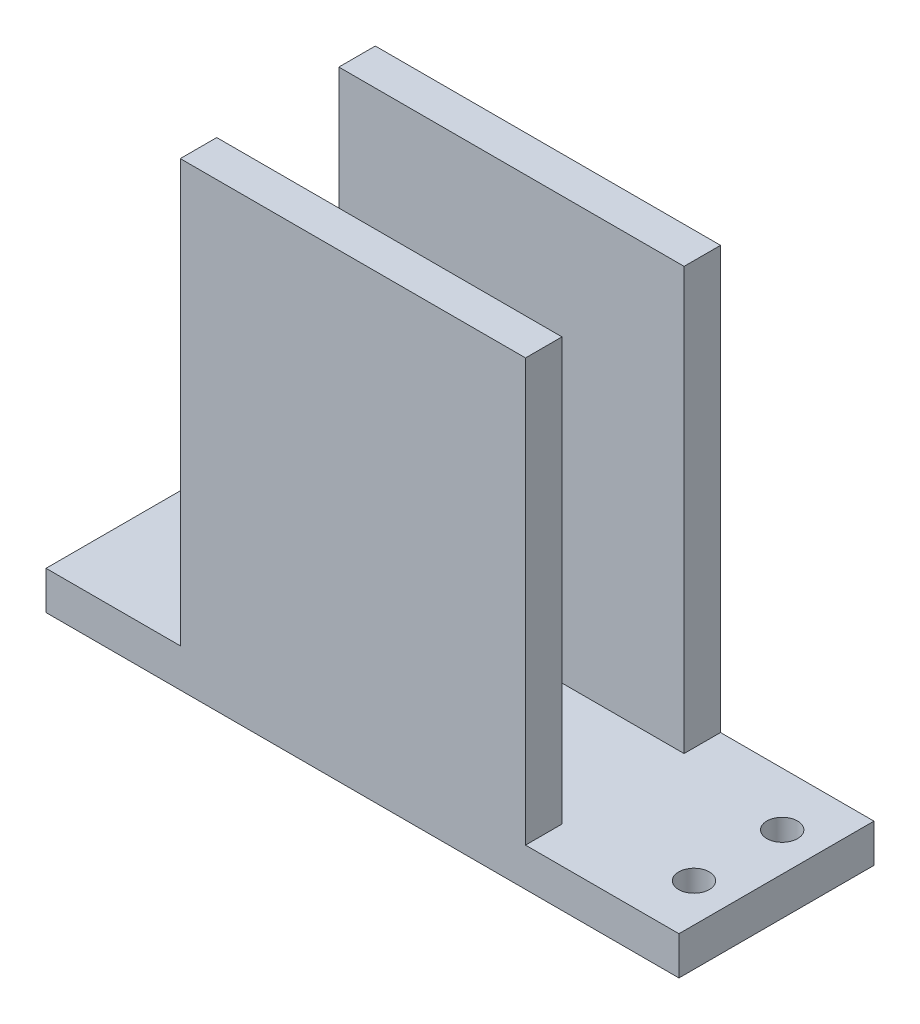
SolidWorks part; units mm, degrees
ref_plane "Front Plane" through (0, 0, 0) normal (0, 0, 1) x (1, 0, 0)
ref_plane "Top Plane" through (0, 0, 0) normal (0, 1, 0) x (1, 0, 0)
ref_plane "Right Plane" through (0, 0, 0) normal (1, 0, 0) x (0, 0, -1)
sketch "Sketch1" plane through (0, 0, 0) normal (0, 1, 0) x (1, 0, 0)
  line L1 (0, 0) -> (165, 0)
  line L2 (0, 0) -> (0, 50.84)
  line L3 (0, 50.84) -> (165, 50.84)
  line L4 (165, 0) -> (165, 50.84)
  dimension "D1" = 165
  dimension "D2" = 50.84
extrude "Boss-Extrude1" add sketch "Sketch1" along normal blind 10
sketch "Sketch2" plane through (0, 10, 0) normal (0, 1, 0) x (1, 0, 0)
  line L0 (0, 25.42) -> (80, 25.42) construction
  line L1 (0, 50.84) -> (0, 0) construction
  line L2 (80, 50.84) -> (80, 0) construction
  line L3 (165, 50.84) -> (0, 50.84) construction
  line L4 (0, 0) -> (165, 0) construction
  line L5 (35, 50.84) -> (125, 50.84)
  line L6 (35, 50.84) -> (35, 40.84)
  line L7 (35, 40.84) -> (125, 40.84)
  line L8 (125, 40.84) -> (125, 50.84)
  line L9 (125, 10) -> (125, 0)
  line L10 (35, 0) -> (125, 0)
  line L11 (35, 0) -> (35, 10)
  line L12 (35, 10) -> (125, 10)
  point P13 (80, 50.84)
  dimension "D1" = 80
  dimension "D2" = 90
  dimension "D3" = 10
extrude "Boss-Extrude2" add sketch "Sketch2" along normal blind 110
sketch "Sketch3" plane through (0, 10, 0) normal (0, 1, 0) x (1, 0, 0)
  line L0 (0, 25.42) -> (165, 25.42) construction
  line L1 (0, 50.84) -> (0, 0) construction
  line L2 (165, 0) -> (165, 50.84) construction
  circle A0 centre (30, 36.92) radius 4
  circle A1 centre (155, 36.92) radius 4
  dimension "D2" = 8
  dimension "D5" = 8
  dimension "D1" = 30
  dimension "D3" = 11.5
  dimension "D4" = 125
extrude "Cut-Extrude1" cut sketch "Sketch3" against normal blind 30
ref_plane "Plane1" through (0, 0, -25.42) normal (0, 0, -1) x (-1, 0, 0)
mirror "Mirror1" about plane through (0, 0, -25.42) normal (0, 0, -1) of "Cut-Extrude1"
sketch "Sketch4" plane through (0, 0, -10) normal (0, 0, -1) x (-1, 0, 0)
  line L1 (-125, 120) -> (-35, 120)
  line L2 (-125, 120) -> (-125, 10)
  line L3 (-125, 10) -> (-35, 10)
  line L4 (-35, 120) -> (-35, 10)
extrude "Cut-Extrude2" cut sketch "Sketch4" against normal blind 0.5
mirror "Mirror2" about plane through (0, 0, -25.42) normal (0, 0, -1) of "Cut-Extrude2"
